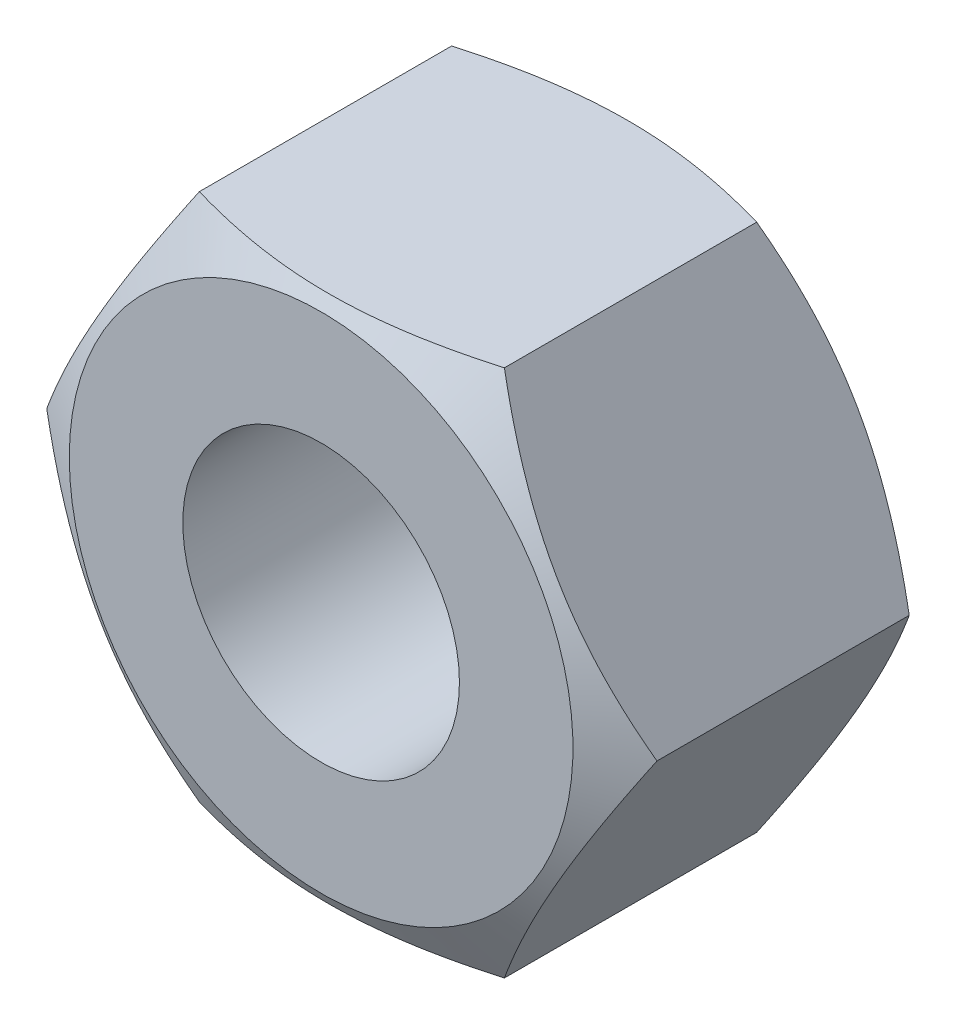
SolidWorks part; units mm, degrees
ref_plane "Front" through (0, 0, 0) normal (0, 0, 1) x (1, 0, 0)
ref_plane "Top" through (0, 0, 0) normal (0, 1, 0) x (1, 0, 0)
ref_plane "Right" through (0, 0, 0) normal (1, 0, 0) x (0, 0, -1)
sketch "Sketch1" plane through (0, 0, 0) normal (0, 0, 1) x (1, 0, 0)
  line L1 (4.6188, -8) -> (9.2376, 0)
  line L2 (9.2376, 0) -> (4.6188, 8)
  line L3 (4.6188, 8) -> (-4.6188, 8)
  line L4 (-4.6188, 8) -> (-9.2376, 0)
  line L5 (-9.2376, 0) -> (-4.6188, -8)
  line L6 (-4.6188, -8) -> (4.6188, -8)
  circle A0 centre (0, 0) radius 8 construction
  circle A1 centre (0, 0) radius 4.188
  dimension "D" = 8.376
  dimension "s" = 16
extrude "BaseNut" add sketch "Sketch1" against normal blind 9.5
cosmetic thread "ThreadCosmetic1" [suppressed] parameters "D"=10
sketch "Sketch2" plane through (0, 0, 0) normal (0, 1, 0) x (1, 0, 0)
  line L0 (-9.2376, 9.5) -> (-7.625, 9.5)
  line L2 (-7.625, 9.5) -> (-9.2376, 8.569)
  line L3 (-9.2376, 8.569) -> (-9.2376, 9.5)
  line L4 (0, 3.3759) -> (0, -9.8171) construction
  line L6 (-9.7712, 4.75) -> (9.8853, 4.75) construction
  line L7 (-9.2376, 0.931) -> (-9.2376, 0)
  line L8 (-7.625, 0) -> (-9.2376, 0.931)
  line L9 (-9.2376, 0) -> (-7.625, 0)
  line L10 (-9.2376, 9.5) -> (-9.2376, 0) construction
  dimension "dw" = 15.25
  dimension "D1" = 30
  dimension "D2" = 4.75
revolve "Double-Chamfer" cut sketch "Sketch2" angle 360 about L4
sketch "Sketch4" plane through (0, 0, 0) normal (0, 1, 0) x (1, 0, 0)
  line L0 (4.8912, 9.5) -> (4.188, 9.094)
  line L1 (4.188, 9.094) -> (3.376, 9.094)
  line L2 (3.376, 9.094) -> (3.376, 9.906)
  line L3 (3.376, 9.906) -> (4.188, 9.906)
  line L4 (4.188, 9.906) -> (4.8912, 9.5)
  line L5 (0, 0) -> (0, 109.7681) construction
  dimension "D1" = 0.812
  dimension "D2" = 8.376
revolve "Cut-Revolve10" [suppressed] cut sketch "Sketch4" angle 360 about L5
pattern_linear "LPattern10" [suppressed] count 11 spacing 0.9744 along (0, 0, -1)
equation "\"dw@Sketch2\" = \"s@Sketch1\"-0.75"
equation "\"D2@Sketch2\" = \"m@BaseNut\" / 2"
equation "\"D2@Sketch4\"=\"D@Sketch1\""
equation "\"D1@Sketch4\" =  (\"D@ThreadCosmetic1\" - \"D2@Sketch4\"  )  / 2"
equation "\"D3@LPattern10\" = \"D1@Sketch4\" * 1.2"
equation "\"D1@LPattern10\" = \"m@BaseNut\" / \"D3@LPattern10\" + 1"
